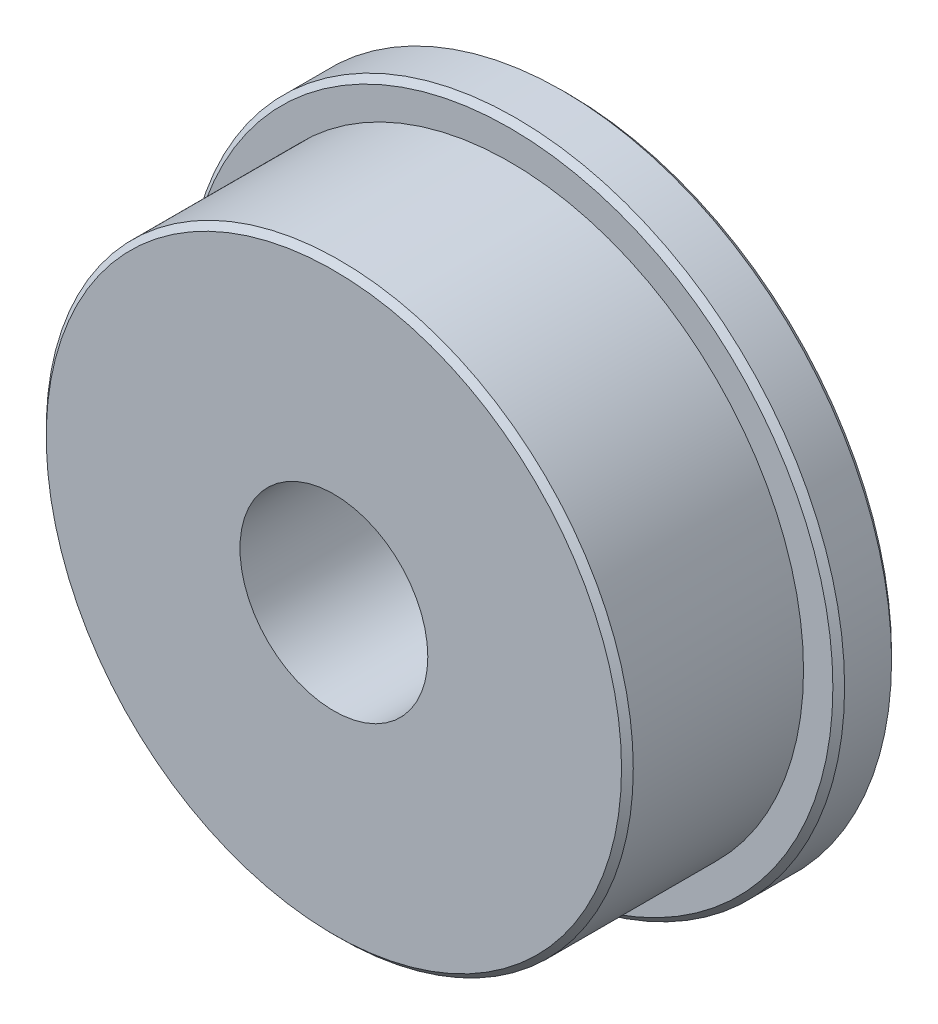
SolidWorks part; units mm, degrees
ref_plane "Alzado" through (0, 0, 0) normal (0, 0, 1) x (1, 0, 0)
ref_plane "Planta" through (0, 0, 0) normal (0, 1, 0) x (1, 0, 0)
ref_plane "Vista lateral" through (0, 0, 0) normal (1, 0, 0) x (0, 0, -1)
sketch "Croquis1" plane through (0, 0, 0) normal (0, 1, 0) x (1, 0, 0)
  line L0 (5, -3.9) -> (5, -1)
  line L1 (5, -1) -> (5.5, -1)
  line L2 (5.5, -1) -> (5.6, -0.9)
  line L3 (5.6, -0.9) -> (5.6, -0.1)
  line L4 (5.6, -0.1) -> (5.5, 0)
  line L5 (5.5, 0) -> (1.6, 0)
  line L6 (1.6, 0) -> (1.6, -4)
  line L7 (1.6, -4) -> (4.9, -4)
  line L8 (4.9, -4) -> (5, -3.9)
  line L9 (0, 0) -> (0, -4) construction
  line L12 (0, -55) -> (0, 55) construction
  line L13 (-55, 0) -> (55, 0) construction
  dimension "D1" = 5.6
  dimension "D2" = 5
  dimension "D3" = 4
  dimension "D4" = 1
  dimension "D5" = 1.6
  dimension "D6" = 0.1
  dimension "D7" = 0.1
  dimension "D9" = 45
  dimension "D10" = 45
  dimension "D11" = 0.1
  dimension "D12" = 45
revolve "Revolución1" add sketch "Croquis1" angle 360 about L9
